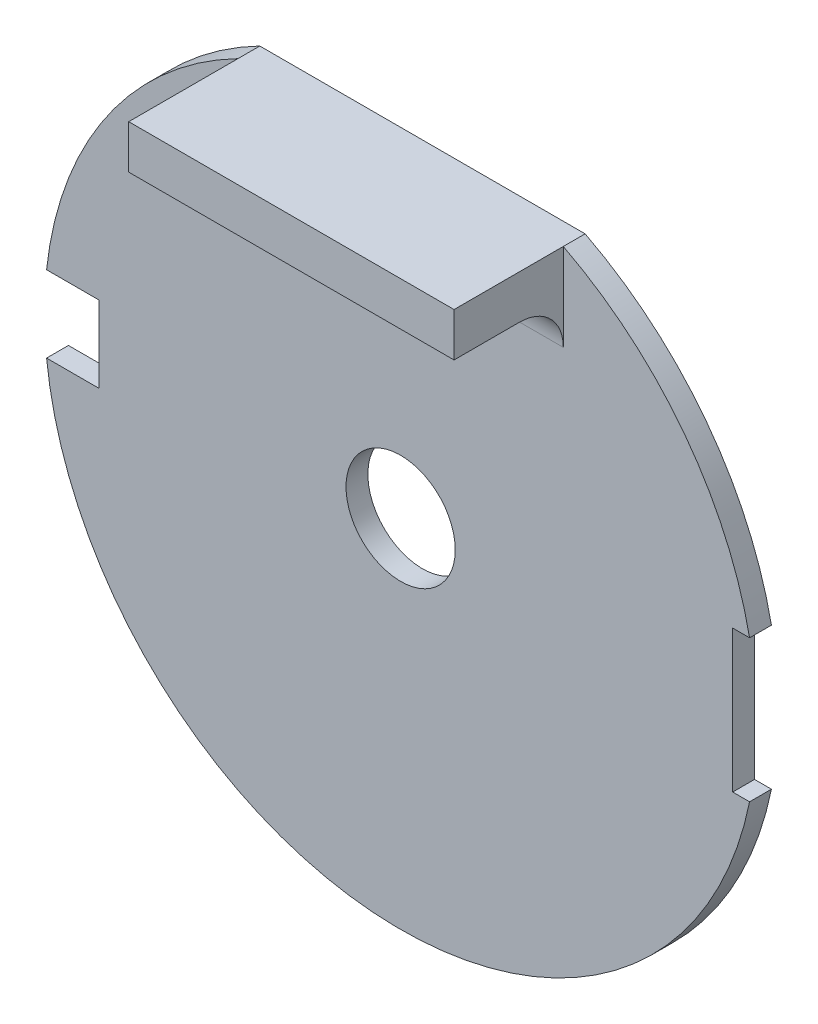
SolidWorks part; units mm, degrees
ref_plane "前视基准面" through (0, 0, 0) normal (0, 0, 1) x (1, 0, 0)
ref_plane "上视基准面" through (0, 0, 0) normal (0, 1, 0) x (1, 0, 0)
ref_plane "右视基准面" through (0, 0, 0) normal (1, 0, 0) x (0, 0, -1)
sketch "草图1" plane through (0, 0, 0) normal (0, 0, 1) x (1, 0, 0)
  line L0 (-7.4458, 14.5) -> (7.4458, 14.5)
  arc A0 (-7.4458, 14.5) -> (7.4458, 14.5) centre (0, 0) ccw
  circle A1 centre (0, 0) radius 2.5
  dimension "D1" = 32.6
  dimension "D2" = 5
  dimension "D3" = 14.5
extrude "凸台-拉伸1" add sketch "草图1" along normal blind 1
sketch "草图2" plane through (0, 0, 1) normal (0, 0, 1) x (1, 0, 0)
  line L0 (-13.8, 1.75) -> (15.2, 1.75) construction
  line L1 (-18.8, 1.75) -> (-13.8, 1.75)
  line L2 (-18.8, 1.75) -> (-18.8, -1.75)
  line L3 (-18.8, -1.75) -> (-13.8, -1.75)
  line L4 (-13.8, 1.75) -> (-13.8, -1.75)
  line L5 (15.2, 1.75) -> (17.8078, 1.75) construction
  line L6 (15.2, 1.75) -> (15.2, -1.75) construction
  line L7 (15.2, -1.75) -> (17.8078, -1.75) construction
  line L8 (17.8078, 1.75) -> (17.8078, -1.75) construction
  line L9 (15.2, -1.75) -> (-13.8, -1.75) construction
  line L11 (15.2, 3.25) -> (17.2, 3.25)
  line L12 (15.2, 3.25) -> (15.2, -3.25)
  line L13 (15.2, -3.25) -> (17.2, -3.25)
  line L14 (17.2, 3.25) -> (17.2, -3.25)
  circle A0 centre (0, 0) radius 16.3 construction
  point P10 (-16.3, 0)
  point P11 (16.3, 0)
  point P13 (-13.8, 0)
  point P17 (17.2, 0)
  dimension "D1" = 29
  dimension "D2" = 2.5
  dimension "D3" = 5
  dimension "D4" = 3.5
  dimension "D5" = 6.5
  dimension "D6" = 2
extrude "切除-拉伸1" cut sketch "草图2" against normal through all
sketch "草图3" plane through (0, 0, 1) normal (0, 0, 1) x (1, 0, 0)
  line L1 (-7.4458, 14.5) -> (7.4458, 14.5)
  line L2 (-7.4458, 14.5) -> (-7.4458, 12.5)
  line L3 (-7.4458, 12.5) -> (7.4458, 12.5)
  line L4 (7.4458, 14.5) -> (7.4458, 12.5)
  dimension "D1" = 2
extrude "凸台-拉伸2" add sketch "草图3" along normal blind 5
fillet "圆角1" radius 2 1 edges at (0, 12.5, 1)
